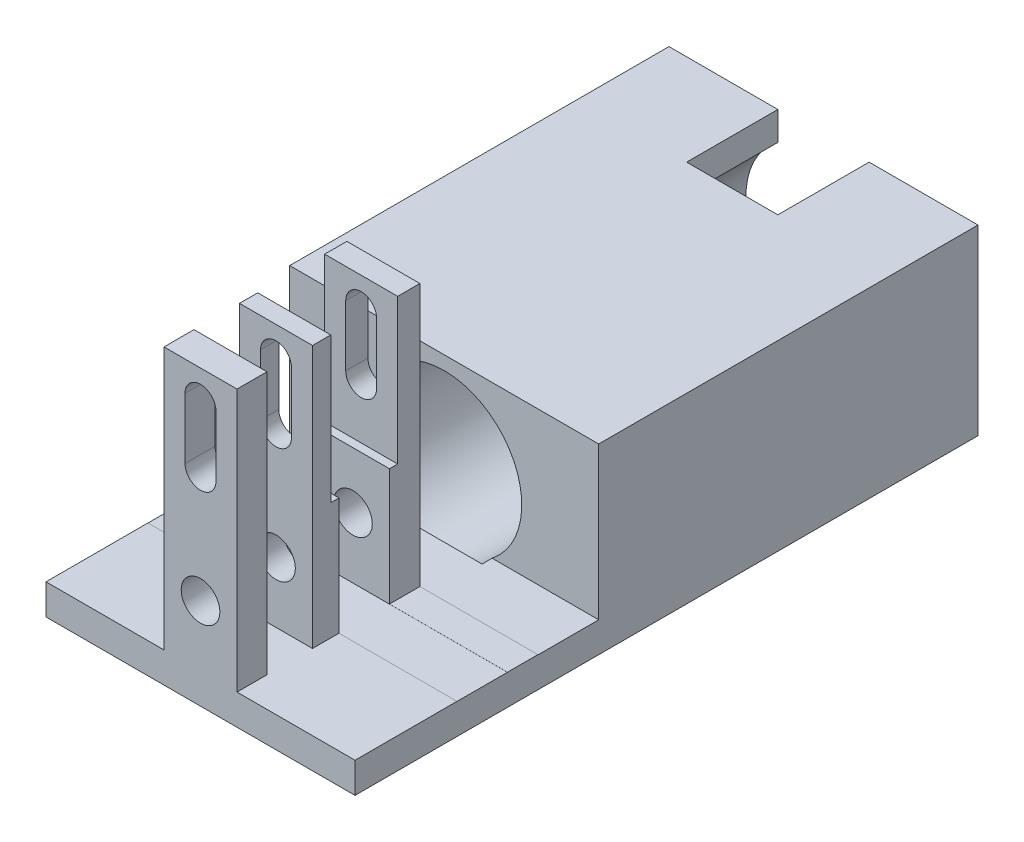
SolidWorks part; units mm, degrees
ref_plane "Front Plane" through (0, 0, 0) normal (0, 0, 1) x (1, 0, 0)
ref_plane "Top Plane" through (0, 0, 0) normal (0, 1, 0) x (1, 0, 0)
ref_plane "Right Plane" through (0, 0, 0) normal (1, 0, 0) x (0, 0, -1)
sketch "Sketch1" plane through (0, 0, 0) normal (0, 1, 0) x (1, 0, 0)
  line L1 (-25.4, -45) -> (25.4, -45)
  line L2 (-25.4, -45) -> (-25.4, 45)
  line L3 (-25.4, 45) -> (25.4, 45)
  line L4 (25.4, -45) -> (25.4, 45)
  line L5 (-25.4, -45) -> (25.4, 45) construction
  line L6 (-25.4, 45) -> (25.4, -45) construction
  point P0 (0, 0)
  dimension "D1" = 50.8
  dimension "D2" = 90
extrude "Main Extrude" add sketch "Sketch1" along normal blind 30
sketch "Sketch2" plane through (0, 0, -45) normal (0, 0, -1) x (-1, 0, 0)
  line L0 (-25.4, 30) -> (25.4, 30) construction
  circle A0 centre (0, 15) radius 12.75
  dimension "D1" = 15
  dimension "D2" = 25.5
extrude "Motor Slot Cut" cut sketch "Sketch2" against normal blind 64
sketch "Sketch3" plane through (25.4, 0, 0) normal (1, 0, 0) x (0, 0, -1)
  line L0 (-45, 30) -> (45, 30) construction
  line L1 (-32.35, 30) -> (-40.65, 30)
  line L2 (-32.35, 30) -> (-32.35, 5)
  line L3 (-32.35, 5) -> (-40.65, 5)
  line L4 (-40.65, 30) -> (-40.65, 5)
  line L5 (-45, 0) -> (45, 0) construction
  line L6 (-45, 30) -> (-45, 0) construction
  dimension "D1" = 5
  dimension "D2" = 4.35
  dimension "D3" = 8.3
extrude "Fillament Throughway cut" cut sketch "Sketch3" against normal through all
sketch "Sketch4" plane through (0, 0, 45) normal (0, 0, 1) x (1, 0, 0)
  line L0 (-25.4, 30) -> (25.4, 30) construction
  circle A0 centre (0, 15) radius 3.175
  dimension "D1" = 6.35
  dimension "D2" = 15
extrude "Bottom Axle Cut" cut sketch "Sketch4" against normal through all
sketch "For Reference Sketch" plane through (0, 0, 45) normal (0, 0, 1) x (1, 0, 0)
  line L0 (0, 15) -> (0, 43.275)
  line L1 (-25.4, 30) -> (25.4, 30) construction
  dimension "D1" = 28.275
  dimension "D2" = 13.275
sketch "Sketch6" plane through (0, 30, 0) normal (0, 1, 0) x (1, 0, 0)
  line L0 (25.4, -32.35) -> (25.4, 45) construction
  line L1 (-25.4, -45) -> (25.4, -45)
  line L2 (-25.4, -45) -> (-25.4, -40.65)
  line L3 (-25.4, -40.65) -> (25.4, -40.65)
  line L4 (25.4, -45) -> (25.4, -40.65)
  line L5 (-25.4, -32.35) -> (25.4, -32.35)
  line L6 (-25.4, -32.35) -> (-25.4, -27.35)
  line L7 (-25.4, -27.35) -> (25.4, -27.35)
  line L8 (25.4, -32.35) -> (25.4, -27.35)
  dimension "D1" = 5
extrude "Top Fins Extrude" add sketch "Sketch6" along normal blind 18.15
sketch "Sketch7" plane through (0, 0, 45) normal (0, 0, 1) x (1, 0, 0)
  line L0 (0, 43.275) -> (0, 33.275) construction
  line L1 (2.54, 43.275) -> (2.54, 33.275)
  line L2 (-2.54, 43.275) -> (-2.54, 33.275)
  line L3 (0, 15) -> (0, 33.275) construction
  arc A1 (2.54, 43.275) -> (-2.54, 43.275) centre (0, 43.275) ccw
  arc A2 (-2.54, 33.275) -> (2.54, 33.275) centre (0, 33.275) ccw
  point P3 (0, 38.275)
  dimension "D1" = 10
  dimension "D2" = 2.54
  dimension "D3" = 18.275
extrude "Top Axle Cut" cut sketch "Sketch7" against normal through all
sketch "Sketch8" plane through (0, 30, 0) normal (0, 1, 0) x (1, 0, 0)
  line L0 (25.4, 45) -> (-25.4, 45) construction
  line L1 (25.4, -27.35) -> (25.4, 45) construction
  line L2 (7.5, 45) -> (-7.5, 45)
  line L3 (7.5, 45) -> (7.5, 30)
  line L4 (7.5, 30) -> (-7.5, 30)
  line L5 (-7.5, 45) -> (-7.5, 30)
  line L6 (-25.4, 45) -> (-25.4, -27.35) construction
  dimension "D1" = 15
  dimension "D2" = 15
  dimension "D3" = 17.9
  dimension "D4" = 17.9
extrude "Wire Hole Cut" cut sketch "Sketch8" against normal blind 8
sketch "Sketch9" plane through (0, 0, 45) normal (0, 0, 1) x (1, 0, 0)
  line L1 (-25.4, 48.15) -> (-6, 48.15)
  line L2 (-25.4, 48.15) -> (-25.4, 5.0097)
  line L3 (-25.4, 5.0097) -> (-6, 5.0097)
  line L4 (-6, 48.15) -> (-6, 5.0097)
  line L5 (25.4, 48.15) -> (6, 48.15)
  line L6 (25.4, 48.15) -> (25.4, 5.0097)
  line L7 (25.4, 5.0097) -> (6, 5.0097)
  line L8 (6, 48.15) -> (6, 5.0097)
  dimension "D1" = 12
  dimension "D2" = 19.4
extrude "EaseOfAccessCut" cut sketch "Sketch9" against normal blind 20
ref_plane "Plane1" through (0, 0, 36.5) normal (0, 0, 1) x (1, 0, 0)
sketch "Sketch10" plane through (0, 0, 36.5) normal (0, 0, 1) x (1, 0, 0)
  line L9 (-12.5, 24.275) -> (12.5, 24.275)
  line L10 (-12.5, 24.275) -> (-12.5, 51.9124)
  line L11 (-12.5, 51.9124) -> (12.5, 51.9124)
  line L12 (12.5, 24.275) -> (12.5, 51.9124)
  line L13 (0, 33.275) -> (0, 30.735) construction
  arc A0 (-2.54, 33.275) -> (2.54, 33.275) centre (0, 33.275) ccw construction
  dimension "D1" = 25
  dimension "D2" = 12.5
  dimension "D3" = 9
extrude "BearingSizeCut" cut sketch "Sketch10" against normal mid plane 11
sketch "Sketch11" plane through (25.4, 0, 0) normal (1, 0, 0) x (0, 0, -1)
  line L5 (-27.35, 30) -> (-17.35, 30)
  line L6 (-27.35, 30) -> (-27.35, 4.9695)
  line L7 (-27.35, 4.9695) -> (-17.35, 4.9695)
  line L8 (-17.35, 30) -> (-17.35, 4.9695)
  dimension "D1" = 10
extrude "Rubber Band Cut" cut sketch "Sketch11" against normal through all
sketch "Sketch12" plane through (0, 0, 45) normal (0, 0, 1) x (1, 0, 0)
  line L1 (-25.4, 0) -> (25.4, 0)
  line L2 (-25.4, 0) -> (-25.4, 5.0097)
  line L3 (-25.4, 5.0097) -> (25.4, 5.0097)
  line L4 (25.4, 0) -> (25.4, 5.0097)
extrude "Boss-Extrude1" add sketch "Sketch12" along normal blind 12.41
sketch "Sketch13" plane through (0, 5.0097, 0) normal (0, 1, 0) x (1, 0, 0)
  line L0 (25.4, -57.41) -> (-25.4, -57.41) construction
  line L1 (-6, -57.41) -> (6, -57.41)
  line L2 (-6, -57.41) -> (-6, -52.4857)
  line L3 (-6, -52.4857) -> (6, -52.4857)
  line L4 (6, -57.41) -> (6, -52.4857)
  line L5 (-6, -42) -> (-6, -45) construction
  line L6 (6, -42) -> (6, -45) construction
  dimension "D1" = 0
  dimension "D2" = 0
extrude "Boss-Extrude2" add sketch "Sketch13" along normal up to surface (43.1403 mm away) up to face at (0, 48.15, 43.5)
sketch "Sketch15" plane through (0, 0, 52.4857) normal (0, 0, -1) x (-1, 0, 0)
  line L0 (0, 33.28) -> (0, 43.28) construction
  line L1 (-2.54, 33.28) -> (-2.54, 43.28)
  line L2 (2.54, 33.28) -> (2.54, 43.28)
  circle A0 centre (0, 15) radius 3.175
  arc A1 (-2.54, 33.28) -> (2.54, 33.28) centre (0, 33.28) ccw
  arc A2 (2.54, 43.28) -> (-2.54, 43.28) centre (0, 43.28) ccw
  point P6 (0, 38.28)
  dimension "D2" = 2.54
  dimension "D1" = 10
  dimension "D3" = 28.28
extrude "Cut-Extrude1" cut sketch "Sketch15" against normal blind 12.41
